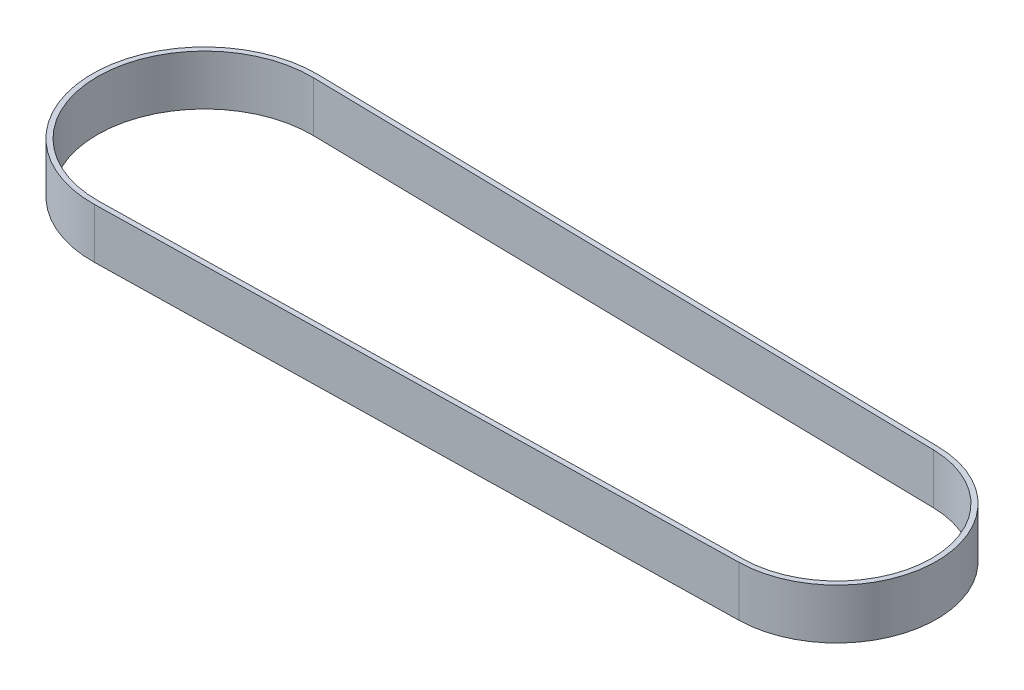
SolidWorks part; units mm, degrees
other "Markup1"
sketch "Sketch2" plane through (-23.4, 0, -23.4) normal (-0.231, -0.9167, -0.326) x (-0.972, 0.232, 0.0366)
sketch "Sketch3" plane through (-22.35, 0, -22.35) normal (-0.231, -0.9167, -0.326) x (-0.972, 0.232, 0.0366)
material "BUTYL"
ref_plane "Front Plane" through (0, 0, 0) normal (0, 0, 1) x (1, 0, 0)
ref_plane "Top Plane" through (0, 0, 0) normal (0, 1, 0) x (1, 0, 0)
ref_plane "Right Plane" through (0, 0, 0) normal (1, 0, 0) x (0, 0, -1)
sketch "Sketch1" plane through (0, 0, 0) normal (0, 1, 0) x (1, 0, 0)
  line L0 (0, 0) -> (126, 0) construction
  line L1 (0.4151, 21.346) -> (126.3675, 18.8964)
  line L2 (0.4346, 22.3458) -> (126.3869, 19.8962)
  line L3 (0.4346, -22.3458) -> (126.3869, -19.8962)
  line L4 (0.4151, -21.346) -> (126.3675, -18.8964)
  arc A0 (0.4151, 21.346) -> (0.4151, -21.346) centre (0, 0) ccw
  arc A1 (126.3675, -18.8964) -> (126.3675, 18.8964) centre (126, 0) ccw
  arc A2 (126.3869, -19.8962) -> (126.3869, 19.8962) centre (126, 0) ccw
  arc A3 (0.4346, 22.3458) -> (0.4346, -22.3458) centre (0, 0) ccw
  dimension "D1" = 42.7
  dimension "D3" = 37.8
  dimension "D2" = 126
  dimension "D4" = 1
extrude "Boss-Extrude1" add sketch "Sketch1" along normal blind 10
